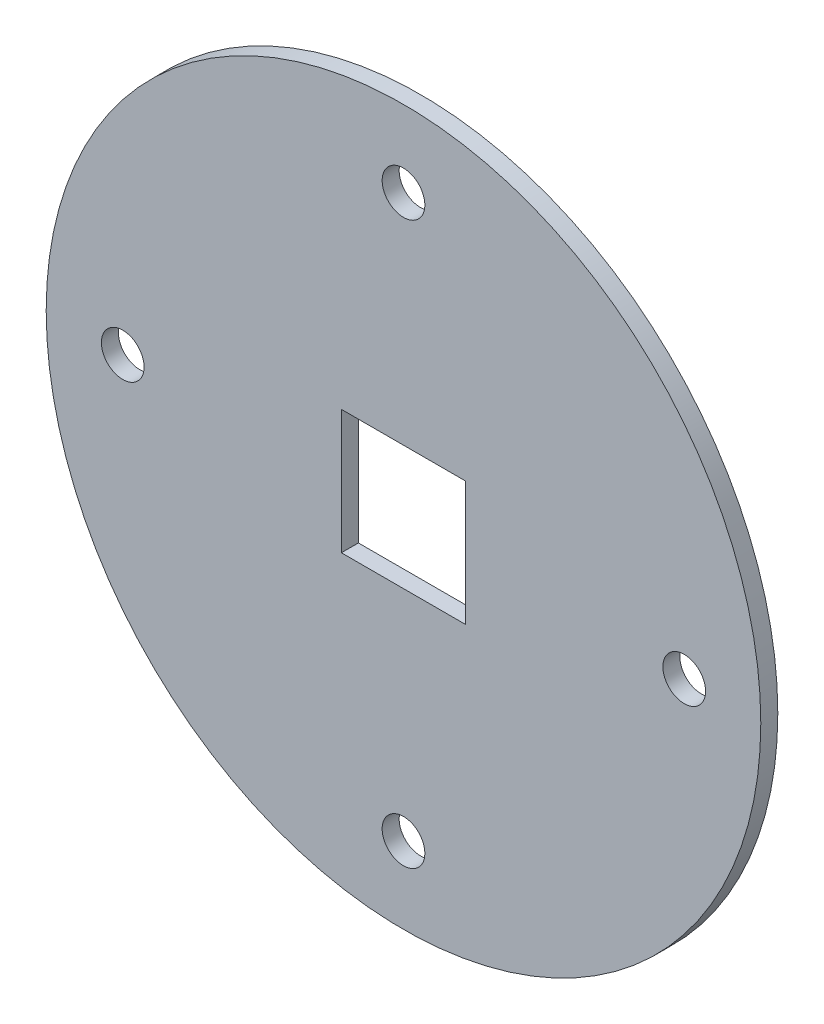
SolidWorks part; units mm, degrees
ref_plane "Ön Düzlem" through (0, 0, 0) normal (0, 0, 1) x (1, 0, 0)
ref_plane "Üst Düzlem" through (0, 0, 0) normal (0, 1, 0) x (1, 0, 0)
ref_plane "Sağ Düzlem" through (0, 0, 0) normal (1, 0, 0) x (0, 0, -1)
sketch "Çizim1" plane through (0, 0, 0) normal (0, 0, 1) x (1, 0, 0)
  line L1 (-36.5, 36.5) -> (36.5, 36.5)
  line L2 (-36.5, 36.5) -> (-36.5, -36.5)
  line L3 (-36.5, -36.5) -> (36.5, -36.5)
  line L4 (36.5, 36.5) -> (36.5, -36.5)
  line L5 (-36.5, 36.5) -> (36.5, -36.5) construction
  line L6 (-36.5, -36.5) -> (36.5, 36.5) construction
  circle A0 centre (0, 0) radius 210
  circle A1 centre (0, 0) radius 165 construction
  circle A2 centre (0, 165) radius 12.55
  circle A3 centre (165, 0) radius 12.55
  circle A4 centre (0, -165) radius 12.55
  circle A5 centre (-165, 0) radius 12.55
  dimension "D3" = 420
  dimension "D4" = 330
  dimension "D5" = 25.1
  dimension "D6" = 25.1
  dimension "D7" = 25.1
  dimension "D8" = 25.1
  dimension "D1" = 73
  dimension "D2" = 73
extrude "Yükseklik-Ekstrüzyon1" add sketch "Çizim1" along normal blind 10
